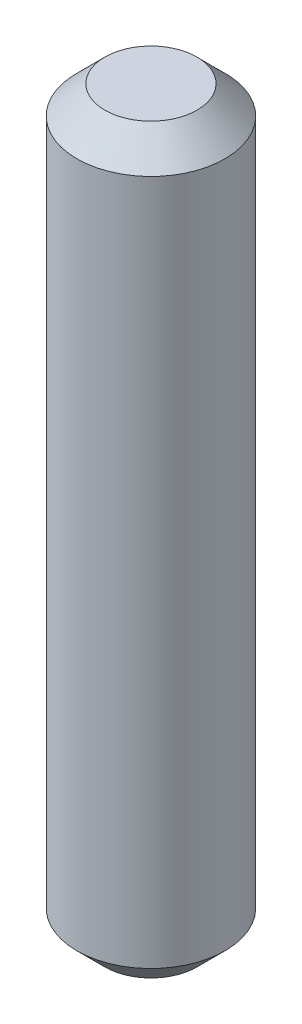
SolidWorks part; units mm, degrees
ref_plane "Alzado" through (0, 0, 0) normal (0, 0, 1) x (1, 0, 0)
ref_plane "Planta" through (0, 0, 0) normal (0, 1, 0) x (1, 0, 0)
ref_plane "Vista lateral" through (0, 0, 0) normal (1, 0, 0) x (0, 0, -1)
sketch "Croquis1" plane through (0, 0, 0) normal (0, 1, 0) x (1, 0, 0)
  circle A0 centre (0, 0) radius 1.585
  dimension "D1" = 3.17
extrude "Saliente-Extruir1" add sketch "Croquis1" along normal mid plane 15.87
chamfer "Chaflán1" distance 0.6 angle 45 2 edges at (0, -7.935, 1.585) (0, 7.935, 1.585)
